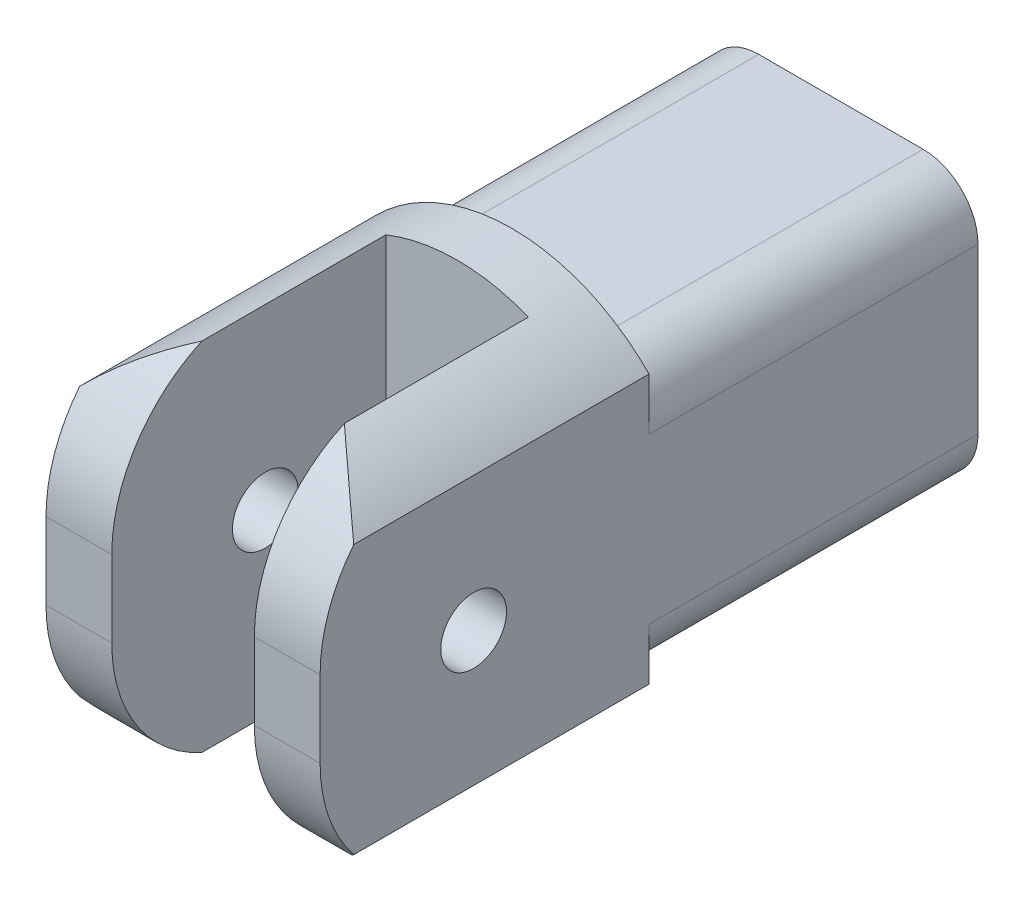
SolidWorks part; units mm, degrees
ref_plane "Front Plane" through (0, 0, 0) normal (0, 0, 1) x (1, 0, 0)
ref_plane "Top Plane" through (0, 0, 0) normal (0, 1, 0) x (1, 0, 0)
ref_plane "Right Plane" through (0, 0, 0) normal (1, 0, 0) x (0, 0, -1)
sketch "Sketch1" plane through (0, 0, 0) normal (1, 0, 0) x (0, 0, -1)
  line L0 (0, 0) -> (204.7864, 0) construction
  line L1 (67.7381, 12.5) -> (37.7381, 12.5)
  line L2 (37.7381, 12.5) -> (37.7381, 17.5)
  line L3 (37.7381, 17.5) -> (21.7381, 17.5)
  line L4 (7.7381, 3.5) -> (7.7381, -3.5)
  line L5 (21.7381, -17.5) -> (37.7381, -17.5)
  line L6 (37.7381, -17.5) -> (37.7381, -12.5)
  line L7 (37.7381, -12.5) -> (67.7381, -12.5)
  line L8 (67.7381, -12.5) -> (67.7381, 12.5)
  arc A0 (7.7381, -3.5) -> (21.7381, -17.5) centre (21.7381, -3.5) ccw
  arc A1 (21.7381, 17.5) -> (7.7381, 3.5) centre (21.7381, 3.5) ccw
  circle A2 centre (21.7381, 0) radius 3
  dimension "D7" = 14
  dimension "D8" = 6
  dimension "D1" = 25
  dimension "D2" = 30
  dimension "D3" = 30
  dimension "D4" = 35
  dimension "D5" = 17.5
  dimension "D6" = 12.5
extrude "Boss-Extrude1" add sketch "Sketch1" along normal blind 25
sketch "Sketch2" plane through (0, 0, -67.7381) normal (0, 0, -1) x (-1, 0, 0)
  line L0 (0, 0) -> (-25, 0) construction
  line L1 (-25, -12.5) -> (-25, 12.5) construction
  circle A0 centre (-12.5, 0) radius 12.5
sketch "Sketch3" plane through (0, 0, -67.7381) normal (0, 0, -1) x (-1, 0, 0)
  circle A0 centre (-12.5, 0) radius 6.4
  point P3 (0, 0)
  point P4 (-12.5, 0)
  dimension "D1" = 12.8
extrude "Cut-Extrude2" cut sketch "Sketch3" against normal blind 108
sketch "Sketch4" plane through (0, 0, -7.7381) normal (0, 0, 1) x (1, 0, 0)
  line L0 (0, 0) -> (25, 0) construction
  line L1 (25, 3.5) -> (25, -3.5) construction
  line L2 (0, 0) -> (25, 0) construction
  line L3 (6, -20.2438) -> (19, -20.2438)
  line L4 (6, -20.2438) -> (6, 20.2438)
  line L5 (6, 20.2438) -> (19, 20.2438)
  line L6 (19, -20.2438) -> (19, 20.2438)
  line L7 (6, -20.2438) -> (19, 20.2438) construction
  line L8 (6, 20.2438) -> (19, -20.2438) construction
  point P5 (12.5, 0)
  point P10 (0, 0)
  point P11 (12.5, 0)
  dimension "D1" = 13
extrude "Cut-Extrude3" cut sketch "Sketch4" against normal blind 25
sketch "Sketch5" plane through (0, 0, -37.7381) normal (0, 0, -1) x (-1, 0, 0)
  circle A0 centre (-12.5, 0) radius 17.5
  point P3 (0, 0)
  point P4 (-12.5, 0)
fillet "Fillet2" radius 5 4 edges at (0, -12.5, -52.7381) (0, 12.5, -52.7381) (25, -12.5, -52.7381) (25, 12.5, -52.7381)
extrude "Cut-Extrude5" cut sketch "Sketch5" against normal blind 39 flip side to cut contours A0
